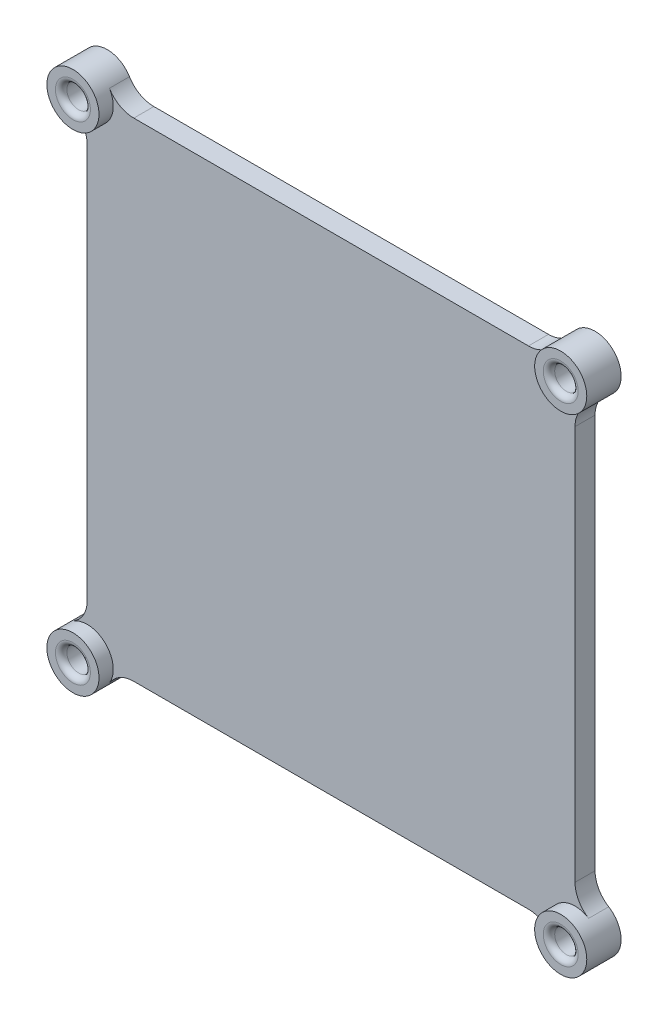
SolidWorks part; units mm, degrees
ref_plane "Front Plane" through (0, 0, 0) normal (0, 0, 1) x (1, 0, 0)
ref_plane "Top Plane" through (0, 0, 0) normal (0, 1, 0) x (1, 0, 0)
ref_plane "Right Plane" through (0, 0, 0) normal (1, 0, 0) x (0, 0, -1)
sketch "Sketch1" plane through (0, 0, 0) normal (0, 0, 1) x (1, 0, 0)
  line L0 (40.1, 0) -> (40.1, -80.2) construction
  line L1 (0, 0) -> (80.2, 0)
  line L2 (0, 0) -> (0, -80.2)
  line L3 (0, -80.2) -> (80.2, -80.2)
  line L4 (80.2, 0) -> (80.2, -80.2)
  line L6 (-2.5, 2.5) -> (82.7, 2.5)
  line L7 (-2.5, 2.5) -> (-2.5, -82.7)
  line L8 (-2.5, -82.7) -> (82.7, -82.7)
  line L9 (82.7, 2.5) -> (82.7, -82.7)
  line L10 (-2.5, 2.5) -> (82.7, -82.7) construction
  line L11 (-2.5, -82.7) -> (82.7, 2.5) construction
  circle A0 centre (-2.5, -82.7) radius 2.05
  circle A1 centre (-2.5, -82.7) radius 4.55
  circle A2 centre (82.7, -82.7) radius 2.05
  circle A3 centre (82.7, -82.7) radius 4.55
  circle A4 centre (82.7, 2.5) radius 2.05
  circle A5 centre (82.7, 2.5) radius 4.55
  circle A6 centre (-2.5, 2.5) radius 2.05
  circle A7 centre (-2.5, 2.5) radius 4.55
  point P7 (40.1, -40.1)
  dimension "D5" = 4.1
  dimension "D8" = 2.5
  dimension "D1" = 80.2
  dimension "D2" = 80.2
  dimension "D3" = 2.5
  dimension "D4" = 2.5
  dimension "D6" = 2
  dimension "D7" = 2
extrude "Boss-Extrude1" add sketch "Sketch1" along normal blind 3.5 contours A7 L7 A1 L2 | A7 L1 A5 L6 | A5 L4 A3 L9 | A3 L3 A1 L8 | L7 A7 L6 A6 | L6 A7 L7 A6 | L6 A5 L9 A4 | L9 A5 L6 A4 | L7 A1 L8 A0 | L8 A1 L7 A0 | L9 A3 L8 A2 | L8 A3 L9 A2 | A7 L2 A1 L3 A3 L4 A5 L1 | L4 A3 L3 | L3 A1 L2 | L2 A7 L1 | L1 A5 L4
fillet "Fillet1" radius 5 8 edges at (-2.5, -78.15, 1.75) (2.05, -82.7, 1.75) (78.15, -82.7, 1.75) (82.7, -78.15, 1.75) (82.7, -2.05, 1.75) (78.15, 2.5, 1.75) (2.05, 2.5, 1.75) (-2.5, -2.05, 1.75)
sketch "Sketch2" plane through (0, 0, 0) normal (0, 0, -1) x (-1, 0, 0)
  circle A0 centre (-82.7, 2.5) radius 4.55
  circle A1 centre (2.5, 2.5) radius 4.55
  circle A2 centre (2.5, -82.7) radius 4.55
  circle A3 centre (-82.7, -82.7) radius 4.55
extrude "Boss-Extrude2" add sketch "Sketch2" against normal blind 1
sketch "Sketch3" plane through (0, 0, 3.5) normal (0, 0, 1) x (1, 0, 0)
  circle A0 centre (-2.5, 2.5) radius 4.55
  circle A1 centre (-2.5, 2.5) radius 2.05
  circle A2 centre (82.7, 2.5) radius 2.05
  circle A3 centre (82.7, 2.5) radius 4.55
  circle A4 centre (82.7, -82.7) radius 2.05
  circle A5 centre (82.7, -82.7) radius 4.55
  circle A6 centre (-2.5, -82.7) radius 2.05
  circle A7 centre (-2.5, -82.7) radius 4.55
  dimension "D1" = 2
  dimension "D2" = 2
extrude "Boss-Extrude3" add sketch "Sketch3" along normal blind 2.5
fillet "Fillet2" radius 1 4 edges at (84.75, 2.5, 6) (84.75, -82.7, 6) (-0.45, -82.7, 6) (-0.45, 2.5, 6)
